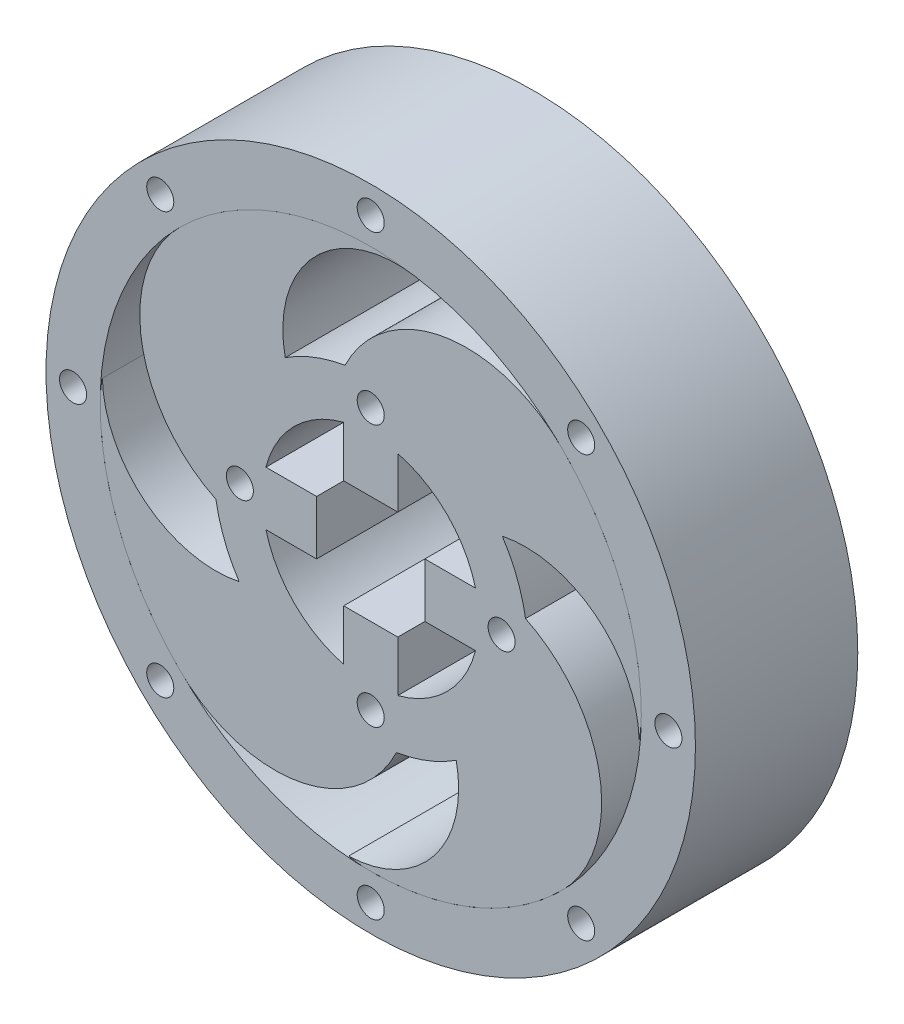
SolidWorks part; units mm, degrees
ref_plane "Front Plane" through (0, 0, 0) normal (0, 0, 1) x (1, 0, 0)
ref_plane "Top Plane" through (0, 0, 0) normal (0, 1, 0) x (1, 0, 0)
ref_plane "Right Plane" through (0, 0, 0) normal (1, 0, 0) x (0, 0, -1)
sketch "Sketch6" plane through (0, 0, 0) normal (0, 0, 1) x (1, 0, 0)
  circle A0 centre (0, 0) radius 20
  circle A1 centre (0, 0) radius 29
  dimension "D1" = 40
  dimension "D2" = 58
extrude "Inner Ring" add sketch "Sketch6" against normal blind 30 separate body
sketch "Sketch7" plane through (0, 0, 0) normal (0, 0, 1) x (1, 0, 0)
  line L2 (-10, 5) -> (-10, -5)
  line L3 (-5, 10) -> (5, 10)
  line L4 (10, 5) -> (10, -5)
  line L5 (-5, -10) -> (5, -10)
  line L14 (-19.3649, 5) -> (-10, 5)
  line L15 (-19.3649, -5) -> (-10, -5)
  line L16 (-5, 19.3649) -> (-5, 10)
  line L17 (5, 19.3649) -> (5, 10)
  line L18 (19.3649, 5) -> (10, 5)
  line L19 (19.3649, -5) -> (10, -5)
  line L20 (5, -19.3649) -> (5, -10)
  line L21 (-5, -19.3649) -> (-5, -10)
  circle A1 centre (0, 0) radius 20
  circle M19 centre (0, 0) radius 20
  dimension "D1" = 20
  dimension "D2" = 20
  dimension "D3" = 10
  dimension "D5" = 10
  dimension "D7" = 10
  dimension "D8" = 10
extrude "Motor Connector Cut" add sketch "Sketch7" against normal blind 30 contours L19 L18 L4 M19 | L17 L16 L3 M19 | L15 L2 L14 M19 | L21 L20 L5 M19
sketch "Sketch8" plane through (0, 0, 0) normal (0, 0, 1) x (1, 0, 0)
  circle A1 centre (0, 24.1825) radius 2.5
  circle A2 centre (24.1825, 0) radius 2.5
  circle A3 centre (0, -24.1825) radius 2.5
  circle A4 centre (-24.1825, 0) radius 2.5
  dimension "D1" = 5
  dimension "D2" = 5
  dimension "D3" = 5
  dimension "D4" = 5
  dimension "D6" = 48.3649
  dimension "D8" = 48.3649
extrude "M3 Holes" cut sketch "Sketch8" against normal blind 100 and the other way blind 38
sketch "Sketch9" plane through (0, 0, 0) normal (0, 0, 1) x (1, 0, 0)
  circle A0 centre (0, 0) radius 50
  circle A1 centre (0, 0) radius 60
  circle A3 centre (0, 55) radius 2.5
  circle A4 centre (-38.8909, 38.8909) radius 2.5
  circle A5 centre (-55, 0) radius 2.5
  circle A6 centre (-38.8909, -38.8909) radius 2.5
  circle A7 centre (0, -55) radius 2.5
  circle A8 centre (38.8909, -38.8909) radius 2.5
  circle A9 centre (55, 0) radius 2.5
  circle A10 centre (38.8909, 38.8909) radius 2.5
  dimension "D1" = 120
  dimension "D2" = 100
  dimension "D3" = 5
  dimension "D4" = 5
  dimension "D5" = 5
  dimension "D6" = 5
  dimension "D7" = 5
  dimension "D8" = 5
  dimension "D9" = 5
  dimension "D10" = 5
  dimension "D11" = 38.8909
  dimension "D12" = 38.8909
  dimension "D13" = 38.8909
sketch "Sketch10" plane through (0, 0, 0) normal (0, 0, 1) x (1, 0, 0)
  circle A0 centre (0, 0) radius 29
  circle A1 centre (0, 29) radius 21
  circle A2 centre (29, 0) radius 21
  circle A3 centre (0, -29) radius 21
  circle A4 centre (-29, 0) radius 21
  circle A5 centre (0, 0) radius 50
  circle A6 centre (-17.7016, 17.7016) radius 24.9662
  circle A7 centre (17.7016, 17.7016) radius 24.9662
  circle A8 centre (17.7016, -17.7016) radius 24.9662
  circle A9 centre (-17.7016, -17.7016) radius 24.9662
  circle A10 centre (-28.6072, 4.7568) radius 21
  circle A11 centre (-28.6072, -4.7568) radius 21
  circle A12 centre (-4.7568, -28.6072) radius 21
  circle A13 centre (4.7568, -28.6072) radius 21
  circle A14 centre (28.6072, -4.7568) radius 21
  circle A15 centre (28.6072, 4.7568) radius 21
  circle A16 centre (4.7568, 28.6072) radius 21
  circle A17 centre (-4.7568, 28.6072) radius 21
extrude "Middle Pattern" add sketch "Sketch10" against normal blind 30 contours A0 A10 A1 | A16 A6 A1 A10 A0 | A10 A17 A4 A0 A1 | A6 A17 A10 A1 | A1 A17 A6 | A16 A17 A1 A6 | A17 A16 A1 | A16 A5 A1 | A2 A16 A15 A1 A0 | A0 A16 A2 | A16 A0 A14 A7 A2 | A16 A2 A7 A15 | A15 A7 A2 | A14 A15 A2 A7 | A15 A14 A2 | A1 A15 A0 | A2 A13 A0 | A3 A14 A13 A2 A0 | A0 A14 A3 | A14 A0 A12 A8 A3 | A14 A3 A8 A13 | A12 A13 A3 A8 | A3 A13 A8 | A13 A12 A3 | A13 A3 A5 | A15 A2 A5 | A17 A1 A5 | A12 A0 A10 A9 A4 | A4 A12 A11 A3 A0 | A0 A12 A4 | A12 A4 A9 A11 | A4 A11 A9 | A10 A11 A4 A9 | A11 A4 A5 | A11 A10 A4 | A4 A17 A0 | A0 A17 A7 A6 | A17 A0 A15 A1 A7 | A15 A16 A7 A1 | A16 A15 A7 | A15 A5 A7 | A0 A15 A8 A7 | A15 A0 A13 A2 A8 | A13 A14 A8 A2 | A14 A13 A8 | A7 A8 A0 | A6 A7 A0 | A13 A5 A8 | A11 A5 A9 | A12 A11 A9 | A11 A12 A9 A3 | A13 A0 A11 A3 A9 | A0 A13 A9 A8 | A3 A11 A0 | A8 A9 A0 | A17 A4 A6 A11 A0 | A17 A10 A6 A4 | A17 A6 A10 | A0 A11 A6 A9 | A0 A9 A6 | A17 A5 A6
extrude "Boss-Extrude1" add sketch "Sketch9" against normal blind 30 separate body
